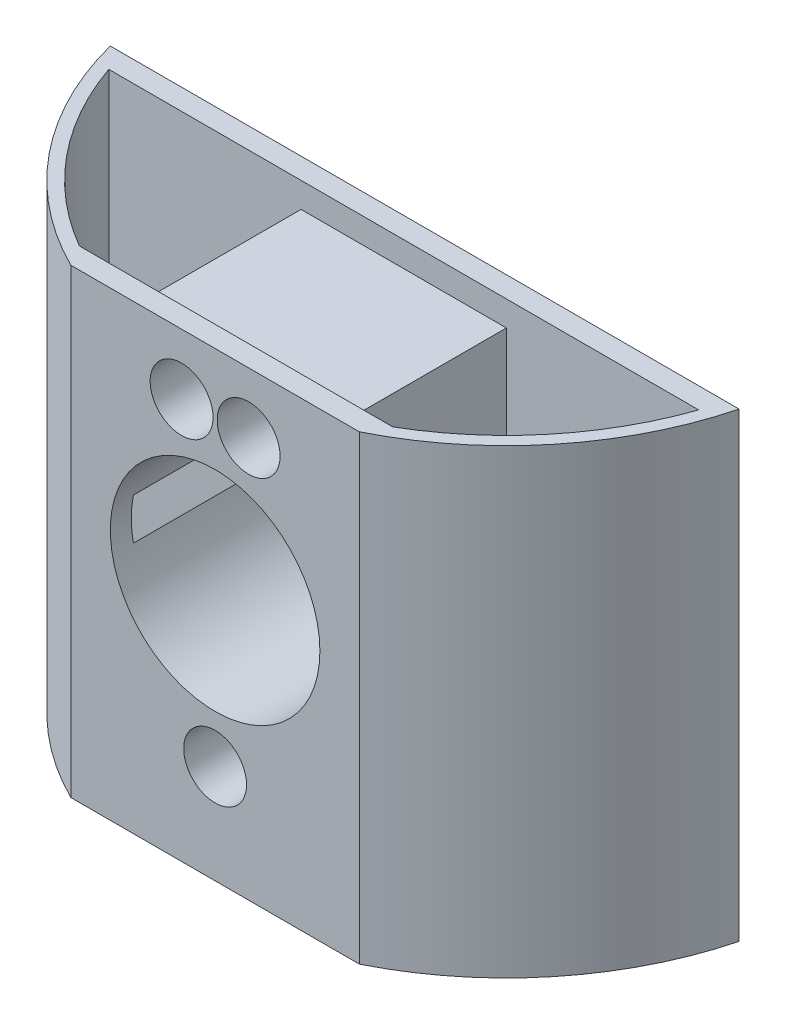
SolidWorks part; units mm, degrees
material "PLA/ABS"
ref_plane "Front Plane" through (0, 0, 0) normal (0, 0, 1) x (1, 0, 0)
ref_plane "Top Plane" through (0, 0, 0) normal (0, 1, 0) x (1, 0, 0)
ref_plane "Right Plane" through (0, 0, 0) normal (1, 0, 0) x (0, 0, -1)
other "Bounding Box"
ref_plane "Default Plane" through (-8.9266, -12.7485, 0) normal (-0.1736, 0.9848, 0) x (0.9848, 0.1736, 0)
sketch "Sketch1" plane through (0, 0, 0) normal (0, 0, 1) x (1, 0, 0)
  line L0 (-25.4, 0) -> (0, 0) construction
  line L1 (-33.9725, 28.575) -> (-16.8275, 28.575) construction
  line L2 (-33.9725, 28.575) -> (-33.9725, -28.575) construction
  line L3 (-33.9725, -28.575) -> (-16.8275, -28.575) construction
  line L4 (-16.8275, 28.575) -> (-16.8275, -28.575) construction
  line L5 (-33.9725, 28.575) -> (-16.8275, -28.575) construction
  line L6 (-33.9725, -28.575) -> (-16.8275, 28.575) construction
  line L8 (41.275, -38.1) -> (-41.275, -38.1)
  line L9 (41.275, -38.1) -> (41.275, 38.1)
  line L10 (41.275, 38.1) -> (-41.275, 38.1)
  line L11 (-41.275, -38.1) -> (-41.275, 38.1)
  line L12 (41.275, -38.1) -> (-41.275, 38.1) construction
  line L13 (41.275, 38.1) -> (-41.275, -38.1) construction
  circle A0 centre (0, 0) radius 44.45 construction
  point P3 (-25.4, 0)
  dimension "D1" = 88.9
  dimension "D2" = 17.145
  dimension "D3" = 57.15
  dimension "D4" = 25.4
  dimension "D5" = 76.2
  dimension "D6" = 82.55
extrude "Boss-Extrude1" add sketch "Sketch1" along normal blind 31.75
sketch "Sketch2" plane through (0, 0, 31.75) normal (0, 0, 1) x (1, 0, 0)
  line L0 (0, -23.114) -> (0, 0) construction
  line L1 (0, 0) -> (5.08, 22.5488) construction
  line L2 (0, 0) -> (-5.08, 22.5488) construction
  line L3 (-5.08, 22.5488) -> (5.08, 22.5488) construction
  line L4 (0, 22.5488) -> (0, 0) construction
  circle A0 centre (0, -23.114) radius 4.7625
  circle A1 centre (-5.08, 22.5488) radius 4.7625
  circle A2 centre (5.08, 22.5488) radius 4.7625
  dimension "D3" = 9.525
  dimension "D1" = 23.114
  dimension "D2" = 10.16
extrude "Cut-Extrude1" cut sketch "Sketch2" against normal through all
sketch "Sketch4" plane through (0, 0, 31.75) normal (0, 0, 1) x (1, 0, 0)
  circle A0 centre (0, 0) radius 15.875
  dimension "D1" = 31.75
extrude "Cut-Extrude3" cut sketch "Sketch4" against normal through all
sketch "Sketch7" plane through (0, 38.1, 0) normal (0, 1, 0) x (1, 0, 0)
  line L0 (0, 0) -> (0, 12.3444) construction
  line L1 (-47.6391, 0) -> (-41.275, 0)
  line L2 (-41.275, 0) -> (-41.275, -14.4557)
  line L3 (-41.275, -31.75) -> (-41.275, 0) construction
  circle A0 centre (0, 12.3444) radius 49.2125 construction
  arc A1 (-47.6391, 0) -> (-41.275, -14.4557) centre (0, 12.3444) ccw
  dimension "D2" = 98.425
  dimension "D1" = 12.3444
extrude "Boss-Extrude3" add sketch "Sketch7" against normal through all
sketch "Sketch6" plane through (0, 38.1, 0) normal (0, 1, 0) x (1, 0, 0)
  line L0 (-41.275, -14.4557) -> (-41.275, -31.75)
  line L1 (-41.275, -31.75) -> (-21.853, -31.75)
  line L2 (41.275, -31.75) -> (-41.275, -31.75) construction
  arc A1 (-41.275, -14.4557) -> (-21.853, -31.75) centre (0, 12.3444) ccw
  arc A2 (-47.6391, 0) -> (-41.275, -14.4557) centre (0, 12.3444) ccw construction
  circle A3 centre (0, 12.3444) radius 49.2125 construction
extrude "Cut-Extrude5" cut sketch "Sketch6" against normal through all
ref_plane "Plane1" through (0, 31.75, 0) normal (0, 1, 0) x (1, 0, 0)
mirror "Mirror2" about plane through (0, 0, 0) normal (1, 0, 0) of "Cut-Extrude5", "Boss-Extrude3"
split "Split1" trim tools "Plane1" bodies to split 117 107 resulting bodies 109 110
delete or keep bodies "Body-Delete/Keep 1" [suppressed] type delete bodies bodies 110
delete or keep bodies "Body-Delete/Keep 2" type delete bodies bodies 109
sketch "Sketch8" plane through (0, 31.75, 0) normal (0, 1, 0) x (1, 0, 0)
  line L0 (-44.6895, -3.175) -> (-15.5575, -3.175)
  line L1 (-15.5575, -3.175) -> (-15.5575, -28.575)
  line L2 (-15.5575, -28.575) -> (-23.7403, -28.575)
  line L3 (47.6391, 0) -> (-47.6391, 0) construction
  line L4 (21.853, -31.75) -> (-21.853, -31.75) construction
  arc A0 (-23.7403, -28.575) -> (-44.6895, -3.175) centre (0, 12.3444) cw
  arc A1 (-47.6391, 0) -> (-21.853, -31.75) centre (0, 12.3444) ccw construction
  dimension "D3" = 1.905
  dimension "D1" = 3.175
  dimension "D2" = 1.27
  dimension "D4" = 3.175
extrude "Cut-Extrude6" cut sketch "Sketch8" against normal offset from surface (62.23 mm away) 7.62 up to face at (0, -38.1, 17.2779)
mirror "Mirror3" about plane through (0, 0, 0) normal (1, 0, 0) of "Cut-Extrude6"
sketch "Sketch9" plane through (0, 0, 3.175) normal (0, 0, 1) x (1, 0, 0)
  line L0 (15.5575, 3.1591) -> (15.5575, 31.75) construction
  line L1 (-15.5575, 3.1591) -> (-15.5575, 31.75) construction
  line L2 (15.5575, 27.94) -> (15.5575, 31.75)
  line L3 (-15.5575, 27.94) -> (-15.5575, 31.75)
  line L4 (-15.5575, 27.94) -> (15.5575, 27.94)
  line L5 (-15.5575, 31.75) -> (15.5575, 31.75)
  circle A0 centre (5.08, 22.5488) radius 4.7625 construction
  circle A1 centre (-5.08, 22.5488) radius 4.7625 construction
  circle A2 centre (5.08, 22.5488) radius 4.7625 construction
  circle A3 centre (-5.08, 22.5488) radius 4.7625 construction
  point P11 (15.5575, 27.94)
  point P14 (-15.5575, 27.94)
  point P15 (-15.1323, 27.94)
  point P16 (15.1676, 27.94)
  dimension "D1" = 3.81
extrude "Cut-Extrude7" cut sketch "Sketch9" along normal up to surface (25.4 mm away) up to face at (-18.338, 0.4233, 28.575)
